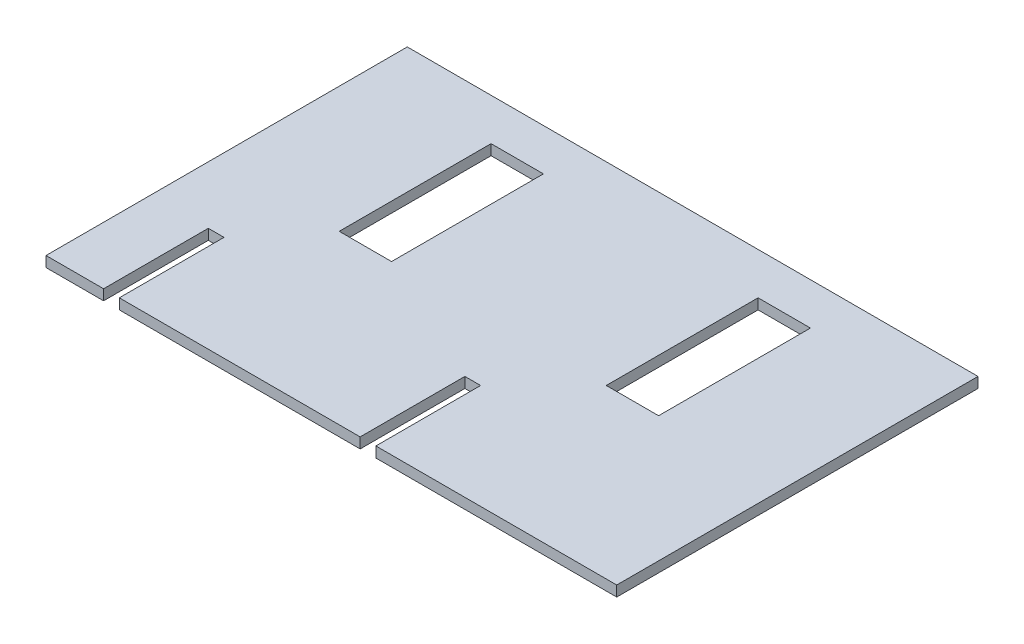
SolidWorks part; units mm, degrees
ref_plane "Front Plane" through (0, 0, 0) normal (0, 0, 1) x (1, 0, 0)
ref_plane "Top Plane" through (0, 0, 0) normal (0, 1, 0) x (1, 0, 0)
ref_plane "Right Plane" through (0, 0, 0) normal (1, 0, 0) x (0, 0, -1)
sketch "Sketch1" plane through (0, 0, 0) normal (0, 1, 0) x (1, 0, 0)
  line L1 (-27.25, 17.25) -> (27.25, 17.25)
  line L2 (-27.25, 17.25) -> (-27.25, -17.25)
  line L3 (-27.25, -17.25) -> (27.25, -17.25)
  line L4 (27.25, 17.25) -> (27.25, -17.25)
  line L5 (-27.25, 17.25) -> (27.25, -17.25) construction
  line L6 (-27.25, -17.25) -> (27.25, 17.25) construction
  point P0 (0, 0)
extrude "Boss-Extrude1" add sketch "Sketch1" along normal blind 1
sketch "Sketch2" plane through (0, 1, 0) normal (0, 1, 0) x (1, 0, 0)
  line L0 (0, 17.25) -> (0, 6)
  line L1 (27.25, 17.25) -> (-27.25, 17.25) construction
sketch "Sketch3" plane through (0, 1, 0) normal (0, 1, 0) x (1, 0, 0)
  line L0 (0, 6) -> (-27.25, 6)
  line L1 (-27.25, 17.25) -> (-27.25, -17.25) construction
sketch "Sketch5" plane through (0, 1, 0) normal (0, 1, 0) x (1, 0, 0)
  line L0 (-27.25, 6) -> (-12.75, 6)
sketch "Sketch6" plane through (0, 1, 0) normal (0, 1, 0) x (1, 0, 0)
  line L1 (-15.25, 13.25) -> (-10.25, 13.25)
  line L2 (-15.25, 13.25) -> (-15.25, -1.25)
  line L3 (-15.25, -1.25) -> (-10.25, -1.25)
  line L4 (-10.25, 13.25) -> (-10.25, -1.25)
  line L5 (-15.25, 13.25) -> (-10.25, -1.25) construction
  line L6 (-15.25, -1.25) -> (-10.25, 13.25) construction
  point P0 (-12.75, 6)
extrude "Cut-Extrude1" cut sketch "Sketch6" against normal blind 2
sketch "Sketch7" plane through (0, 1, 0) normal (0, 1, 0) x (1, 0, 0)
  line L0 (0, 6) -> (27.25, 6)
  line L1 (27.25, -17.25) -> (27.25, 17.25) construction
sketch "Sketch8" plane through (0, 1, 0) normal (0, 1, 0) x (1, 0, 0)
  line L0 (27.25, 6) -> (12.75, 6)
sketch "Sketch9" plane through (0, 1, 0) normal (0, 1, 0) x (1, 0, 0)
  line L1 (10.25, 13.25) -> (15.25, 13.25)
  line L2 (10.25, 13.25) -> (10.25, -1.25)
  line L3 (10.25, -1.25) -> (15.25, -1.25)
  line L4 (15.25, 13.25) -> (15.25, -1.25)
  line L5 (10.25, 13.25) -> (15.25, -1.25) construction
  line L6 (10.25, -1.25) -> (15.25, 13.25) construction
  point P0 (12.75, 6)
extrude "Cut-Extrude2" cut sketch "Sketch9" against normal blind 2
sketch "Sketch10" plane through (0, 1, 0) normal (0, 1, 0) x (1, 0, 0)
  line L0 (-27.25, -17.25) -> (-21.75, -17.25)
  line L1 (-27.25, -17.25) -> (27.25, -17.25) construction
sketch "Sketch11" plane through (0, 1, 0) normal (0, 1, 0) x (1, 0, 0)
  line L0 (-21.75, -17.25) -> (-20.25, -17.25)
  line L1 (-27.25, -17.25) -> (27.25, -17.25) construction
sketch "Sketch12" plane through (0, 1, 0) normal (0, 1, 0) x (1, 0, 0)
  line L0 (-20.25, -17.25) -> (2.75, -17.25)
  line L1 (-27.25, -17.25) -> (27.25, -17.25) construction
sketch "Sketch27" plane through (0, 1, 0) normal (0, 1, 0) x (1, 0, 0)
  line L0 (-21.75, -17.25) -> (-21.75, -7.25)
  line L1 (-21.75, -7.25) -> (-20.25, -7.25)
  line L2 (-20.25, -7.25) -> (-20.25, -17.25)
  line L3 (-20.25, -17.25) -> (-21.75, -17.25)
extrude "Cut-Extrude3" cut sketch "Sketch27" against normal blind 2
sketch "Sketch37" plane through (0, 1, 0) normal (0, 1, 0) x (1, 0, 0)
  line L0 (2.75, -17.25) -> (4.25, -17.25)
  line L1 (-20.25, -17.25) -> (27.25, -17.25) construction
  line L2 (2.75, -17.25) -> (2.75, -7.25)
  line L3 (2.75, -7.25) -> (4.25, -7.25)
  line L4 (4.25, -7.25) -> (4.25, -17.25)
extrude "Cut-Extrude10" cut sketch "Sketch37" against normal blind 2
